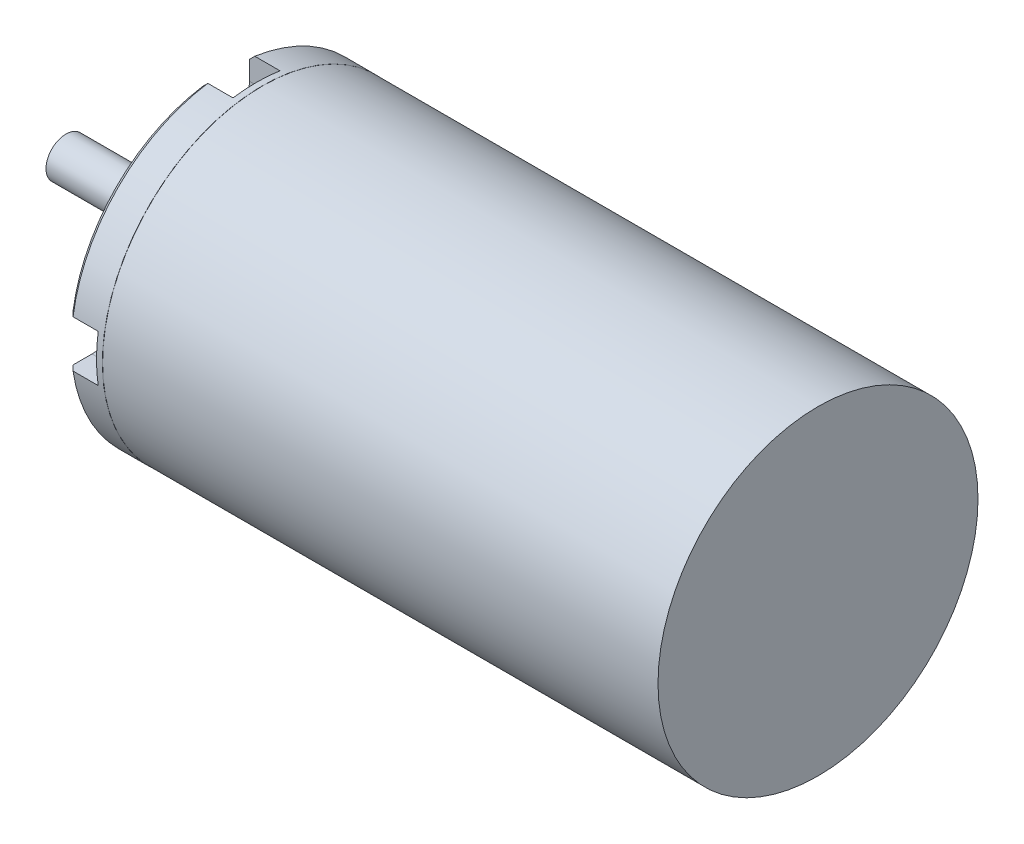
SolidWorks part; units mm, degrees
material "Orange anodized aluminum"
ref_plane "Front Plane" through (0, 0, 0) normal (0, 0, 1) x (1, 0, 0)
ref_plane "Top Plane" through (0, 0, 0) normal (0, 1, 0) x (1, 0, 0)
ref_plane "Right Plane" through (0, 0, 0) normal (1, 0, 0) x (0, 0, -1)
sketch "Sketch3" plane through (0, 0, 0) normal (0, 1, 0) x (1, 0, 0)
  line L0 (-44.1614, 0) -> (113.9195, 0) construction
sketch "Sketch1" plane through (0, 0, 0) normal (1, 0, 0) x (0, 0, -1)
  circle A0 centre (0, 0) radius 20
  dimension "D1" = 40
extrude "Boss-Extrude1" add sketch "Sketch1" along normal blind 74
sketch "Sketch5" plane through (0, 0, 0) normal (0, 1, 0) x (1, 0, 0)
  line L0 (0, 19.3378) -> (0.6622, 20)
  line L1 (0, 20) -> (0, -20) construction
  line L2 (74, 20) -> (0, 20) construction
  line L3 (0.6622, 20) -> (0.6622, 20.1762)
  line L4 (0.6622, 20.1762) -> (4.5501, 20.1762)
  line L5 (4.5501, 20.1762) -> (4.5501, 19.93)
  line L6 (4.5501, 19.93) -> (4.5729, 19.93)
  line L7 (4.5729, 19.93) -> (4.5729, 20.7076)
  line L8 (4.5729, 20.7076) -> (0.4899, 20.7076)
  line L9 (0.4899, 20.7076) -> (-0.8799, 19.3378)
  line L10 (-0.8799, 19.3378) -> (0, 19.3378)
  line L11 (-44.1614, 0) -> (113.9195, 0) construction
  line L12 (0, 0) -> (0.6451, 0)
  line L13 (0.0818, 3.4163) -> (0, 3.4981)
  line L14 (0.0818, 3.4163) -> (0.6451, 3.4163)
  line L15 (0.6451, 0) -> (0.6451, 3.4163)
  line L16 (0, 3.4981) -> (-0.3477, 3.4981)
  line L17 (-0.3477, 3.4981) -> (-0.3477, 0)
  line L18 (-0.3477, 0) -> (0, 0)
revolve "Cut-Revolve1" cut sketch "Sketch5" angle 360 about L0
sketch "Sketch2" plane through (0, 0, 0) normal (-1, 0, 0) x (0, 0, 1)
  circle A0 centre (0, 0) radius 2.5
extrude "Boss-Extrude2" add sketch "Sketch2" along normal blind 20 and the other way up to next
sketch "Sketch6" plane through (0, 0, 0) normal (-1, 0, 0) x (0, 0, 1)
  line L0 (0, 0) -> (0, 16.742) construction
  line L1 (-2.9347, 16.742) -> (-2.9347, 20.7668)
  line L2 (-2.9347, 20.7668) -> (2.9347, 20.7668)
  line L3 (2.9347, 20.7668) -> (2.9347, 16.742)
  line L4 (0, 0) -> (16.742, 0) construction
  line L5 (20.7668, -2.9347) -> (16.742, -2.9347)
  line L6 (20.7668, 2.9347) -> (20.7668, -2.9347)
  line L7 (16.742, 2.9347) -> (20.7668, 2.9347)
  line L8 (0, 0) -> (0, -16.742) construction
  line L9 (-2.9347, -20.7668) -> (-2.9347, -16.742)
  line L10 (2.9347, -20.7668) -> (-2.9347, -20.7668)
  line L11 (2.9347, -16.742) -> (2.9347, -20.7668)
  line L12 (0, 0) -> (-16.742, 0) construction
  line L13 (-20.7668, 2.9347) -> (-16.742, 2.9347)
  line L14 (-20.7668, -2.9347) -> (-20.7668, 2.9347)
  line L15 (-16.742, -2.9347) -> (-20.7668, -2.9347)
  arc A0 (-2.9347, 16.742) -> (2.9347, 16.742) centre (0, 16.742) ccw
  arc A1 (-2.9347, 16.742) -> (2.9347, 16.742) centre (0, 16.742) cw construction
  arc A2 (16.742, 2.9347) -> (16.742, -2.9347) centre (16.742, 0) ccw
  arc A3 (16.742, 2.9347) -> (16.742, -2.9347) centre (16.742, 0) cw construction
  arc A4 (2.9347, -16.742) -> (-2.9347, -16.742) centre (0, -16.742) ccw
  arc A5 (2.9347, -16.742) -> (-2.9347, -16.742) centre (0, -16.742) cw construction
  arc A6 (-16.742, -2.9347) -> (-16.742, 2.9347) centre (-16.742, 0) ccw
  arc A7 (-16.742, -2.9347) -> (-16.742, 2.9347) centre (-16.742, 0) cw construction
  dimension "D1" = 4
extrude "Cut-Extrude1" cut sketch "Sketch6" against normal blind 3.81
sketch "Sketch7" plane through (0, 0, 0) normal (-1, 0, 0) x (0, 0, 1)
  line L0 (0, 0) -> (-3.3981, 12.6818) construction
  line L1 (0, 0) -> (0, 12.5495) construction
  circle A0 centre (-3.3981, 12.6818) radius 1.526
  circle A1 centre (9.2837, 9.2837) radius 1.526
  circle A2 centre (12.6818, -3.3981) radius 1.526
  circle A3 centre (3.3981, -12.6818) radius 1.526
  circle A4 centre (-9.2837, -9.2837) radius 1.526
  circle A5 centre (-12.6818, 3.3981) radius 1.526
  dimension "D1" = 15
  dimension "D2" = 6
extrude "Cut-Extrude2" cut sketch "Sketch7" against normal blind 8.89
